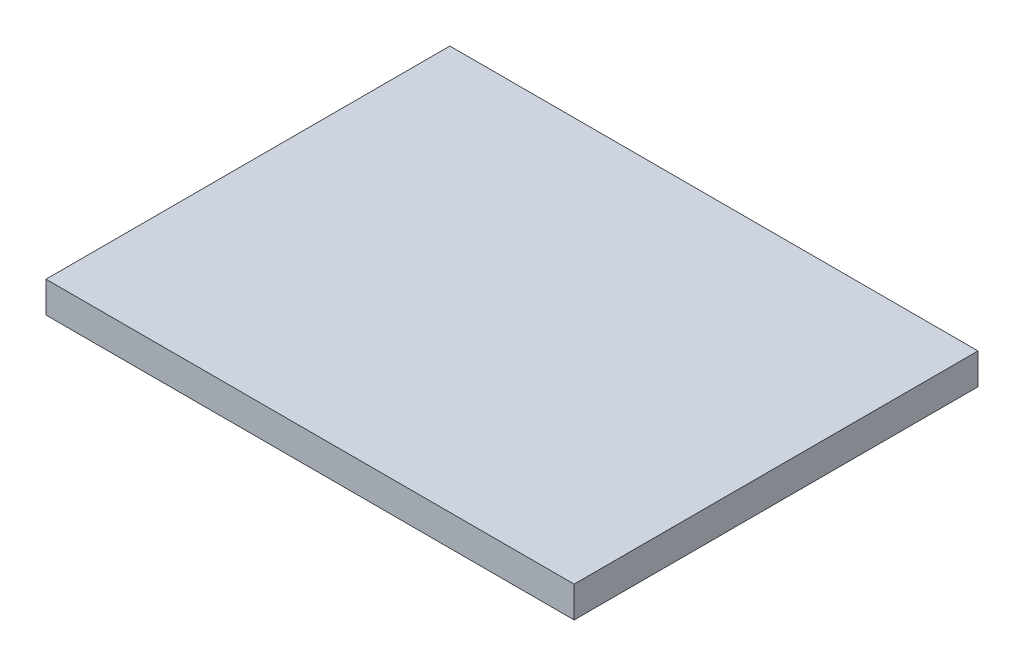
SolidWorks part; units mm, degrees
ref_plane "Alzado" through (0, 0, 0) normal (0, 0, 1) x (1, 0, 0)
ref_plane "Planta" through (0, 0, 0) normal (0, 1, 0) x (1, 0, 0)
ref_plane "Vista lateral" through (0, 0, 0) normal (1, 0, 0) x (0, 0, -1)
sketch "Croquis1" plane through (0, 0, 0) normal (0, 1, 0) x (1, 0, 0)
  line L1 (-40.8626, 37.4885) -> (44.1374, 37.4885)
  line L2 (-40.8626, 37.4885) -> (-40.8626, -27.5115)
  line L3 (-40.8626, -27.5115) -> (44.1374, -27.5115)
  line L4 (44.1374, 37.4885) -> (44.1374, -27.5115)
  dimension "D1" = 65
  dimension "D2" = 85
extrude "Saliente-Extruir1" add sketch "Croquis1" along normal blind 5
